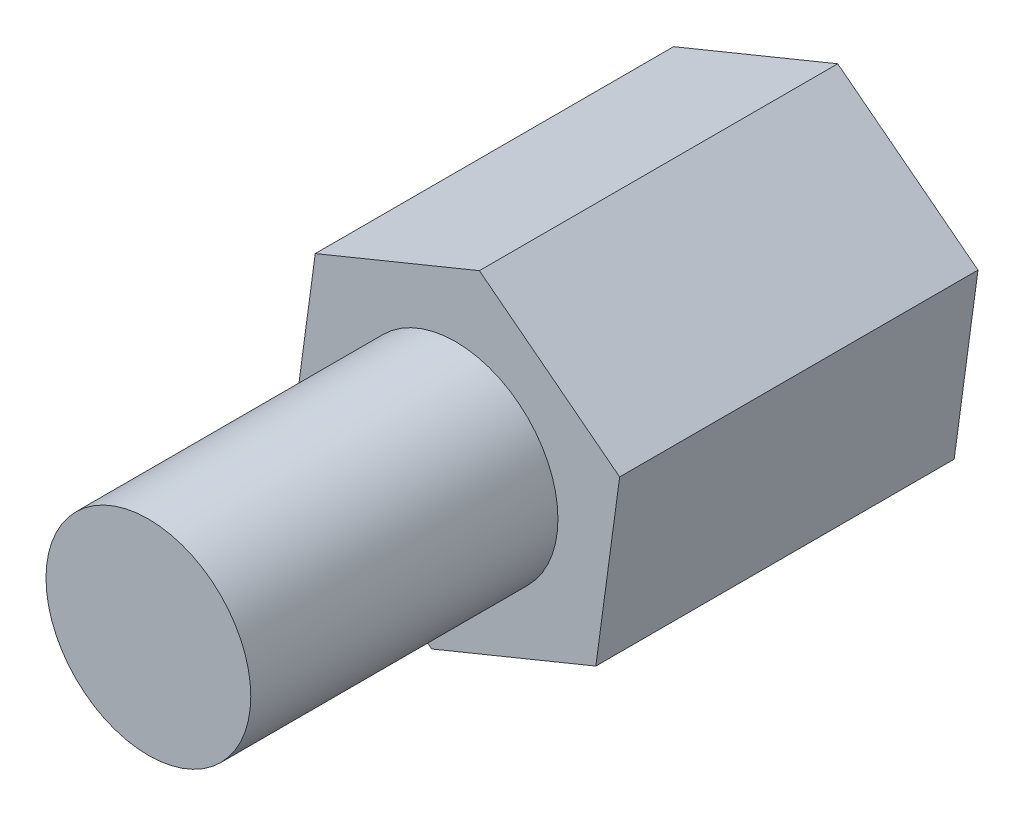
SolidWorks part; units mm, degrees
ref_plane "前视基准面" through (0, 0, 0) normal (0, 0, 1) x (1, 0, 0)
ref_plane "上视基准面" through (0, 0, 0) normal (0, 1, 0) x (1, 0, 0)
ref_plane "右视基准面" through (0, 0, 0) normal (1, 0, 0) x (0, 0, -1)
sketch "草图1" plane through (0, 0, 0) normal (0, 0, 1) x (1, 0, 0)
  line L1 (2.7402, -2.1193) -> (3.2054, 1.3134)
  line L2 (3.2054, 1.3134) -> (0.4652, 3.4327)
  line L3 (0.4652, 3.4327) -> (-2.7402, 2.1193)
  line L4 (-2.7402, 2.1193) -> (-3.2054, -1.3134)
  line L5 (-3.2054, -1.3134) -> (-0.4652, -3.4327)
  line L6 (-0.4652, -3.4327) -> (2.7402, -2.1193)
  circle A0 centre (0, 0) radius 3 construction
  dimension "D1" = 6
extrude "凸台-拉伸1" add sketch "草图1" along normal blind 7
sketch "草图2" plane through (0, 0, 7) normal (0, 0, 1) x (1, 0, 0)
  line L6 (-0.4652, -3.4327) -> (2.7402, -2.1193)
  line L7 (2.7402, -2.1193) -> (3.2054, 1.3134)
  line L8 (3.2054, 1.3134) -> (0.4652, 3.4327)
  line L9 (0.4652, 3.4327) -> (-2.7402, 2.1193)
  line L10 (-2.7402, 2.1193) -> (-3.2054, -1.3134)
  line L11 (-3.2054, -1.3134) -> (-0.4652, -3.4327)
  line L12 (-0.4652, -3.4327) -> (2.7402, -2.1193)
  line L13 (2.7402, -2.1193) -> (3.2054, 1.3134)
  line L14 (3.2054, 1.3134) -> (0.4652, 3.4327)
  line L15 (0.4652, 3.4327) -> (-2.7402, 2.1193)
  line L16 (-2.7402, 2.1193) -> (-3.2054, -1.3134)
  line L17 (-3.2054, -1.3134) -> (-0.4652, -3.4327)
  circle A0 centre (0, 0) radius 2
  dimension "D2" = 4
  dimension "D1" = 0
extrude "凸台-拉伸2" add sketch "草图2" along normal blind 6 contours A0
sketch "草图3" plane through (0, 0, 0) normal (0, 0, -1) x (-1, 0, 0)
  circle A0 centre (0, 0) radius 2
  dimension "D1" = 4
extrude "切除-拉伸1" cut sketch "草图3" against normal blind 4
